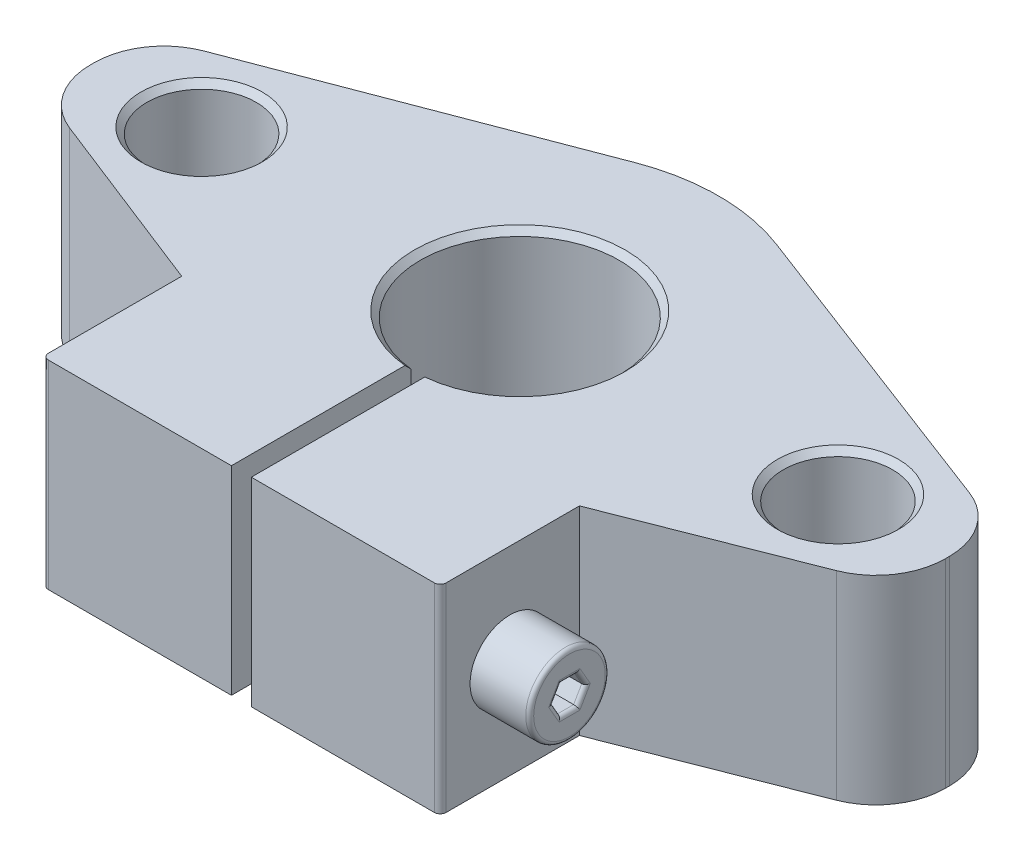
SolidWorks part; units mm, degrees
other "Kamera1"
material "АМг 2 ГОСТ 4784-97"
ref_plane "Front Plane" through (0, 0, 0) normal (0, 0, 1) x (1, 0, 0)
ref_plane "Top Plane" through (0, 0, 0) normal (0, 1, 0) x (1, 0, 0)
ref_plane "Right Plane" through (0, 0, 0) normal (1, 0, 0) x (0, 0, -1)
sketch "Sketch1" plane through (0, 0, 0) normal (0, 1, 0) x (1, 0, 0)
  line L0 (21.5, 0.1007) -> (21.5, -0.1007)
  line L1 (-21.5, 0.1007) -> (-21.5, -0.1007)
  line L2 (0, 10) -> (0, -14) construction
  line L3 (-21.5, 0) -> (21.5, 0) construction
  line L10 (16, -13.3465) -> (16, 13.603) construction
  line L13 (-16, -13.3465) -> (-16, 13.603) construction
  line L15 (0.5, -4.9749) -> (0.5, -14)
  line L20 (0.5, -14) -> (10, -14)
  line L24 (10, -14) -> (10, -7)
  line L25 (-10, -14) -> (-10, -7)
  line L26 (-0.5, -14) -> (-10, -14)
  line L27 (-0.5, -4.9749) -> (-0.5, -14)
  line L28 (19.2786, -3.3588) -> (10, -7)
  line L29 (19.2456, 3.3715) -> (3.5588, 9.3453)
  line L30 (-19.2456, 3.3715) -> (-3.5588, 9.3453)
  line L31 (-19.2786, -3.3588) -> (-10, -7)
  arc A0 (21.5, -0.1007) -> (19.2786, -3.3588) centre (18, -0.1007) cw
  arc A1 (21.5, 0.1007) -> (19.2456, 3.3715) centre (18, 0.1007) ccw
  circle A2 centre (-16, 0) radius 2.75
  circle A3 centre (16, 0) radius 2.75
  arc A4 (-21.5, -0.1007) -> (-19.2786, -3.3588) centre (-18, -0.1007) ccw
  arc A5 (-21.5, 0.1007) -> (-19.2456, 3.3715) centre (-18, 0.1007) cw
  arc A12 (-3.5588, 9.3453) -> (3.5588, 9.3453) centre (0, 0) cw
  arc A13 (-0.5, -4.9749) -> (0.5, -4.9749) centre (0, 0) cw
  point P5 (-21.5, 13.3465)
  point P6 (-21.5, -13.603)
  point P7 (21.5, 13.3465)
  point P8 (21.5, -13.603)
  point P20 (0, 10)
  point P22 (21.5, -2.487)
  point P26 (21.5, 2.513)
  dimension "D1" = 43
  dimension "D4" = 1
  dimension "D7" = 5.5
  dimension "D8" = 16
  dimension "D6" = 24
  dimension "D2" = 5
  dimension "D5" = 7
  dimension "D11" = 3.5
  dimension "D9" = 5
  dimension "D10" = 10
  dimension "D3" = 20
extrude "Boss-Extrude1" add sketch "Sketch1" along normal blind 10
sketch "Sketch3" plane through (10, 0, 0) normal (1, 0, 0) x (0, 0, -1)
  line L1 (-7, 5) -> (-14, 5) construction
  line L2 (-7, 10) -> (-7, 0) construction
  line L3 (-14, 10) -> (-14, 0) construction
  line L4 (-10.5, 10) -> (-10.5, 0) construction
  line L5 (-14, 10) -> (-7, 10) construction
  line L6 (-14, 0) -> (-7, 0) construction
  circle A0 centre (-10.5, 5) radius 2
  point P15 (-10.5, 5)
  dimension "D1" = 4
extrude "Cut-Extrude1" cut sketch "Sketch3" against normal through all
sketch "Esboço1" plane through (10, 0, 0) normal (-1, 0, 0) x (0, 0, 1)
  circle A0 centre (10.5, 5) radius 2 construction
  circle A1 centre (10.5, 5) radius 2
  dimension "D1" = 4
extrude "Ressalto-extrusão2" add sketch "Esboço1" along normal blind 13 and the other way blind 3
sketch "Esboço2" plane through (13, 0, 0) normal (-1, 0, 0) x (0, 0, 1)
  line L0 (8.5, 5) -> (12.5, 5) construction
  line L2 (11.3155, 5) -> (10.9078, 5.7063)
  line L3 (10.9078, 5.7063) -> (10.0922, 5.7063)
  line L4 (10.0922, 5.7063) -> (9.6845, 5)
  line L5 (9.6845, 5) -> (10.0922, 4.2937)
  line L6 (10.0922, 4.2937) -> (10.9078, 4.2937)
  line L7 (10.9078, 4.2937) -> (11.3155, 5)
  circle A0 centre (10.5, 5) radius 2 construction
  circle A2 centre (10.5, 5) radius 0.7063 construction
  point P5 (10.5, 5)
extrude "Corte-extrusão1" cut sketch "Esboço2" along normal blind 5 from surface at 0 contours L7 L6 L5 L4 L3 L2 starting at face at (13, 5, 12.5)
fillet "Filete1" radius 0.2 7 edges at (13, 5, 12.5) (13, 5.3531, 11.1117) (13, 5.7063, 10.5) (13, 5.3531, 9.8883) (13, 4.6469, 9.8883) (13, 4.2937, 10.5) (13, 4.6469, 11.1117)
fillet "Filete2" radius 0.25 1 edges at (-3, 5, 12.5)
chamfer "Фаска1" distance 0.3 angle 45 6 edges at (-16, 0, 2.75) (0, 0, -5) (16, 0, 2.75) (16, 10, 2.75) (-16, 10, 2.75) (0, 10, -5)
fillet "Скругление1" radius 0.3 2 edges at (-10, 5, 14) (10, 5, 14)
